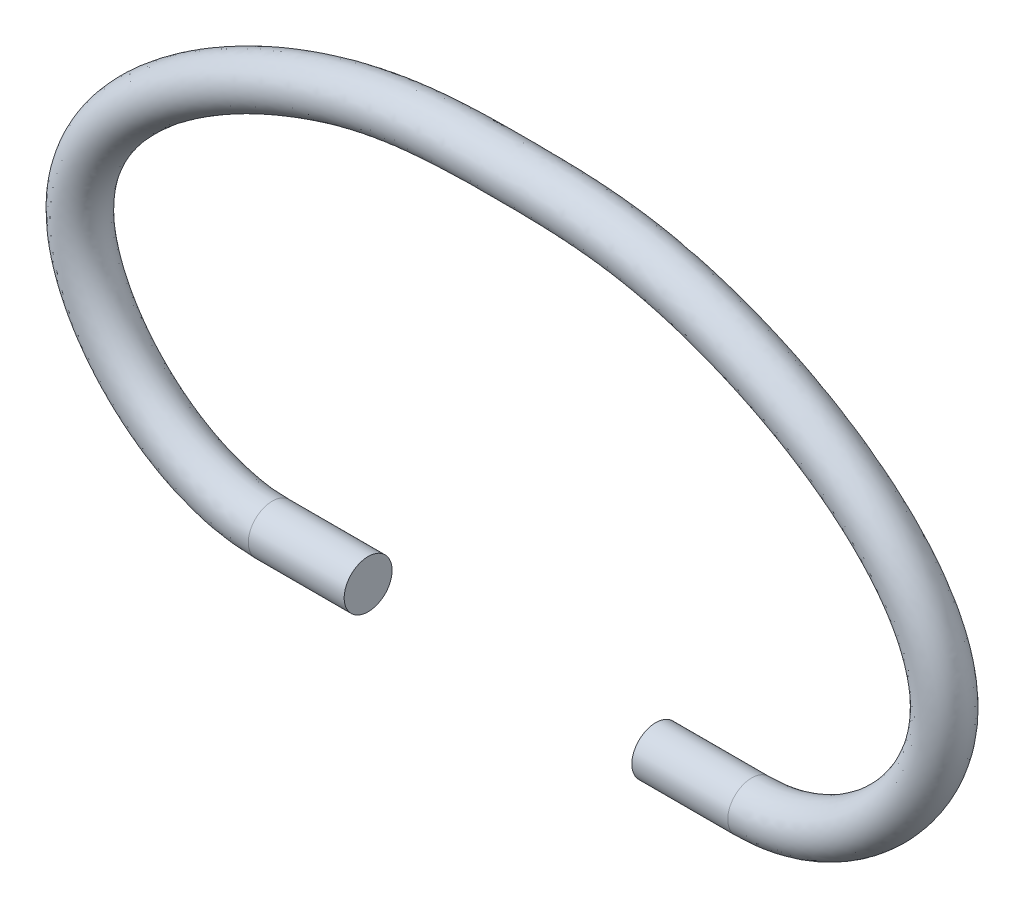
SolidWorks part; units mm, degrees
ref_plane "Alzado" through (0, 0, 0) normal (0, 0, 1) x (1, 0, 0)
ref_plane "Planta" through (0, 0, 0) normal (0, 1, 0) x (1, 0, 0)
ref_plane "Vista lateral" through (0, 0, 0) normal (1, 0, 0) x (0, 0, -1)
sketch "Croquis1" plane through (0, 0, 0) normal (0, 0, 1) x (1, 0, 0)
  line L0 (-3, 0) -> (-5, 0)
  line L1 (3, 0) -> (5, 0)
  spline S0 degree 3 poles (-5, 0) (-7.0052, 0) (-11.5595, 4.5807) (-4.5071, 8.9378) (0.0002, 9.017) (4.5054, 8.9378) (11.573, 4.5807) (6.9867, 0) (5, 0) knots 0 0 0 0 0.163058 0.407646 0.5 0.592354 0.836942 1 1 1 1
  dimension "D1" = 6
  dimension "D2" = 3
  dimension "D3" = 2
  dimension "D4" = 2
  dimension "D5" = 9
  dimension "D6" = 8.75
  dimension "D7" = 3.5
  dimension "D8" = 9
  dimension "D9" = 9
ref_plane "Plano1" through (3, 0, 0) normal (1, 0, 0) x (0, 0, -1)
sketch "Croquis2" plane through (3, 0, 0) normal (1, 0, 0) x (0, 0, -1)
  circle A0 centre (0, 0) radius 0.5
  dimension "D1" = 1
sweep "Barrer1" add profiles "Croquis2" path "Croquis1"
